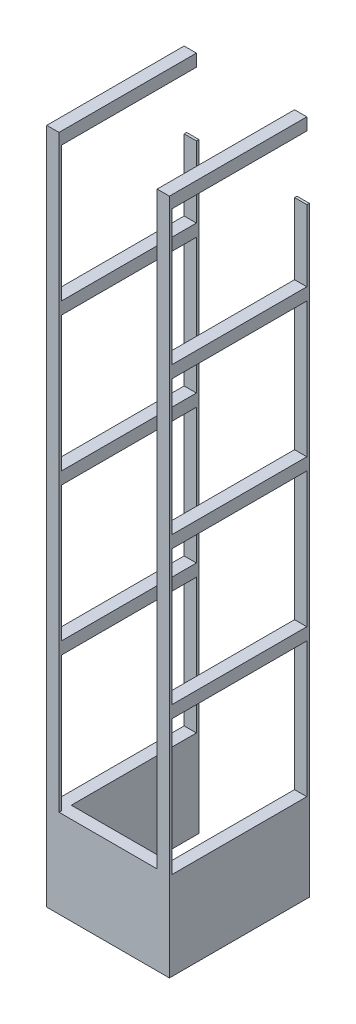
SolidWorks part; units mm, degrees
ref_plane "Front Plane" through (0, 0, 0) normal (0, 0, 1) x (1, 0, 0)
ref_plane "Top Plane" through (0, 0, 0) normal (0, 1, 0) x (1, 0, 0)
ref_plane "Right Plane" through (0, 0, 0) normal (1, 0, 0) x (0, 0, -1)
sketch "Sketch1" plane through (0, 0, 0) normal (0, 0, 1) x (1, 0, 0)
  line L1 (-5, -1) -> (5, -1)
  line L2 (-5, -1) -> (-5, 1)
  line L3 (-5, 1) -> (5, 1)
  line L4 (5, -1) -> (5, 1)
  line L5 (-5, -1) -> (5, 1) construction
  line L6 (-5, 1) -> (5, -1) construction
  point P0 (0, 0)
  dimension "D1" = 2
  dimension "D2" = 10
extrude "Boss-Extrude1" add sketch "Sketch1" along normal blind 112
sketch "Sketch2" plane through (0, 1, 0) normal (0, 1, 0) x (1, 0, 0)
  line L0 (5, -112) -> (5, 0) construction
  line L1 (-5, -112) -> (5, -112)
  line L2 (-5, -112) -> (-5, -110)
  line L3 (-5, -110) -> (5, -110)
  line L4 (5, -112) -> (5, -110)
  dimension "D1" = 2
extrude "Boss-Extrude2" add sketch "Sketch2" along normal blind 480
sketch "Sketch3" plane through (5, 0, 0) normal (1, 0, 0) x (0, 0, -1)
  line L0 (-110, 1) -> (0, 1) construction
  line L1 (-112, -1) -> (-102, -1)
  line L2 (-112, -1) -> (-112, 1)
  line L3 (-112, 1) -> (-102, 1)
  line L4 (-102, -1) -> (-102, 1)
  dimension "D1" = 10
extrude "Boss-Extrude3" add sketch "Sketch3" along normal blind 90
sketch "Sketch4" plane through (0, 0, 102) normal (0, 0, -1) x (-1, 0, 0)
  line L0 (-95, -1) -> (-5, -1) construction
  line L1 (-95, 1) -> (-85, 1)
  line L2 (-95, 1) -> (-95, -1)
  line L3 (-95, -1) -> (-85, -1)
  line L4 (-85, 1) -> (-85, -1)
  dimension "D1" = 10
extrude "Boss-Extrude4" add sketch "Sketch4" along normal blind 102
sketch "Sketch5" plane through (0, 1, 0) normal (0, 1, 0) x (1, 0, 0)
  line L1 (95, -112) -> (85, -112)
  line L2 (95, -112) -> (95, -110)
  line L3 (95, -110) -> (85, -110)
  line L4 (85, -112) -> (85, -110)
  dimension "D1" = 2
  dimension "D2" = 10
extrude "Boss-Extrude5" add sketch "Sketch5" along normal blind 480
sketch "Sketch6" plane through (0, 0, 110) normal (0, 0, -1) x (-1, 0, 0)
  line L0 (-95, 1) -> (-95, 111) construction
  line L1 (-95, 481) -> (-95, 1) construction
  line L2 (5, 481) -> (5, 1) construction
  line L3 (-95, 111) -> (5, 111)
  line L4 (-95, 111) -> (-95, 121)
  line L5 (-95, 121) -> (5, 121)
  line L6 (5, 111) -> (5, 121)
  line L7 (-85, 121) -> (-85, 111)
  line L8 (-85, 481) -> (-85, 1) construction
  line L9 (-5, 121) -> (-5, 111)
  line L10 (-5, 481) -> (-5, 1) construction
  line M4 (-85, 1) -> (-85, 481)
  line M6 (-95, 481) -> (-95, 1)
  dimension "D1" = 110
  dimension "D2" = 10
extrude "Boss-Extrude6" add sketch "Sketch6" along normal blind 110 contours L5 L3 M6 M4 | L5 L9 L3 L6
sketch "Sketch7" plane through (0, 0, 110) normal (0, 0, -1) x (-1, 0, 0)
  line L0 (-95, 121) -> (-95, 231) construction
  line L1 (-95, 481) -> (-95, 121) construction
  line L2 (5, 481) -> (5, 121) construction
  line L3 (-95, 231) -> (5, 231)
  line L4 (-95, 231) -> (-95, 241)
  line L5 (-95, 241) -> (5, 241)
  line L6 (5, 231) -> (5, 241)
  line L7 (-85, 241) -> (-85, 231)
  line L8 (-85, 481) -> (-85, 121) construction
  line L9 (-5, 241) -> (-5, 231)
  line L10 (-5, 481) -> (-5, 121) construction
  line M3 (-95, 481) -> (-95, 121)
  line M5 (-85, 121) -> (-85, 481)
  dimension "D1" = 110
  dimension "D2" = 10
extrude "Boss-Extrude7" add sketch "Sketch7" along normal blind 110 contours L5 L3 M3 M5 | L5 L9 L3 L6
sketch "Sketch8" plane through (0, 0, 110) normal (0, 0, -1) x (-1, 0, 0)
  line L0 (-95, 241) -> (-95, 351)
  line L1 (5, 481) -> (5, 241) construction
  line L2 (-95, 351) -> (5, 351)
  line L3 (-95, 351) -> (-95, 361)
  line L4 (-95, 361) -> (5, 361)
  line L5 (5, 351) -> (5, 361)
  line L6 (-85, 361) -> (-85, 351)
  line L7 (-85, 481) -> (-85, 241) construction
  line L8 (-5, 361) -> (-5, 351)
  line L9 (-5, 481) -> (-5, 241) construction
  line M2 (-95, 481) -> (-95, 241)
  line M4 (-85, 241) -> (-85, 481)
  dimension "D1" = 110
  dimension "D2" = 10
extrude "Boss-Extrude8" add sketch "Sketch8" along normal blind 110 contours L4 L2 M2 M4 | L4 L8 L2 L5
sketch "Sketch9" plane through (0, 0, 110) normal (0, 0, -1) x (-1, 0, 0)
  line L0 (-95, 361) -> (-95, 471) construction
  line L1 (-85, 481) -> (-85, 471)
  line L2 (-95, 471) -> (5, 471)
  line L3 (-95, 471) -> (-95, 481)
  line L4 (-95, 481) -> (5, 481)
  line L5 (5, 471) -> (5, 481)
  line L6 (-85, 481) -> (-85, 361) construction
  line L7 (-5, 481) -> (-5, 471)
  line L8 (-5, 481) -> (-5, 361) construction
  line M2 (-95, 481) -> (-95, 361)
  line M4 (-85, 361) -> (-85, 481)
  line M5 (-85, 481) -> (-95, 481)
  dimension "D1" = 110
extrude "Boss-Extrude9" add sketch "Sketch9" along normal blind 110 contours L2 M2 M4 M5 | L4 L7 L2 L5
sketch "Sketch11" plane through (0, -1, 0) normal (0, -1, 0) x (1, 0, 0)
  line L1 (-5, 112) -> (95, 112)
  line L2 (-5, 112) -> (-5, 0)
  line L3 (-5, 0) -> (95, 0)
  line L4 (95, 112) -> (95, 0)
  line L5 (5, 0) -> (85, 0)
  line L6 (5, 0) -> (5, 102)
  line L7 (5, 102) -> (85, 102)
  line L8 (85, 0) -> (85, 102)
  line M1 (-5, 0) -> (5, 0)
  line M2 (5, 0) -> (5, 102)
  line M3 (5, 102) -> (85, 102)
  line M4 (85, 102) -> (85, 0)
  line M5 (85, 0) -> (95, 0)
  line M6 (95, 0) -> (95, 112)
  line M7 (95, 112) -> (-5, 112)
  line M8 (-5, 112) -> (-5, 0)
extrude "Boss-Extrude10" add sketch "Sketch11" along normal blind 70 contours M8 M1 M2 M3 M4 M5 M6 M7
sketch "Sketch12" plane through (0, -71, 0) normal (0, -1, 0) x (1, 0, 0)
  line L1 (-5, 0) -> (95, 0)
  line L2 (-5, 0) -> (-5, -2)
  line L3 (-5, -2) -> (95, -2)
  line L4 (95, 0) -> (95, -2)
  line L9 (5, 0) -> (85, 0)
  line L10 (5, 0) -> (5, -2)
  line L11 (5, -2) -> (85, -2)
  line L12 (85, 0) -> (85, -2)
  line M10 (-5, 0) -> (5, 0)
  line M14 (85, 0) -> (95, 0)
  dimension "D1" = 2
extrude "Boss-Extrude11" add sketch "Sketch12" against normal blind 490 contours L12 L3 L4 M14 | L10 L2 L3 M10
